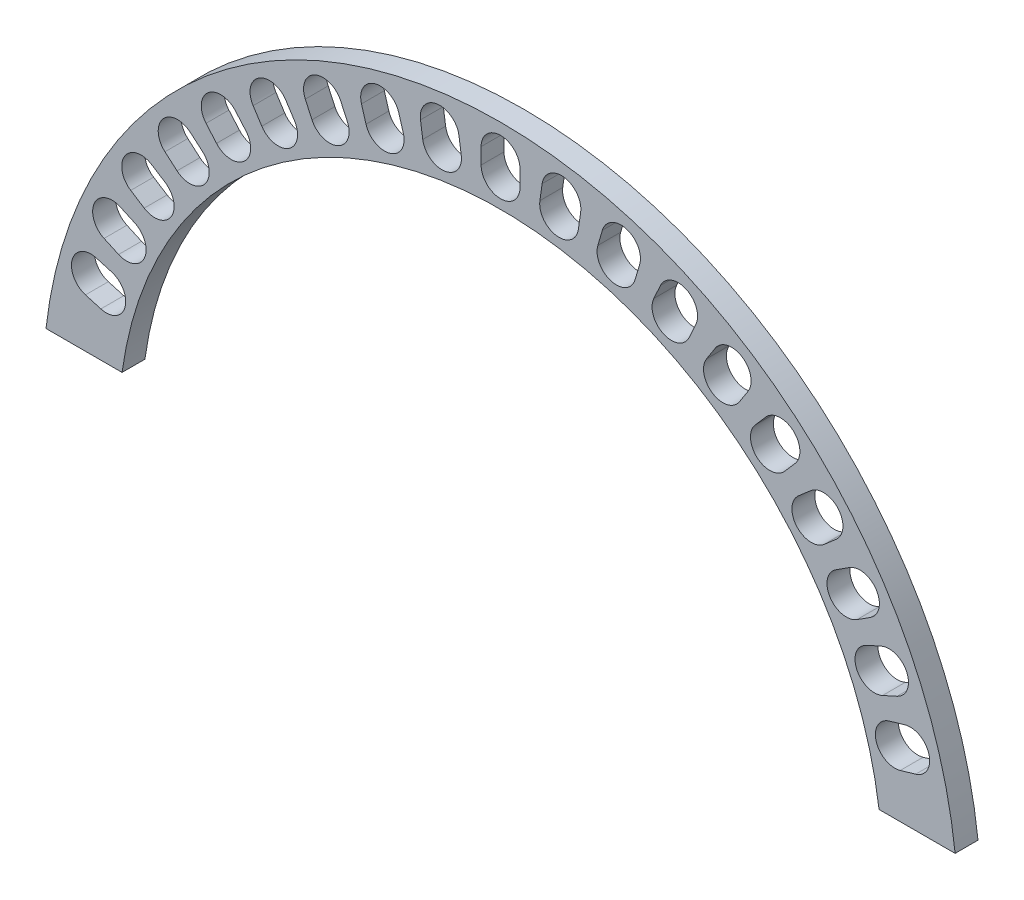
SolidWorks part; units mm, degrees
material "Acier allié"
ref_plane "Plan de face" through (0, 0, 0) normal (0, 0, 1) x (1, 0, 0)
ref_plane "Plan de dessus" through (0, 0, 0) normal (0, 1, 0) x (1, 0, 0)
ref_plane "Plan de droite" through (0, 0, 0) normal (1, 0, 0) x (0, 0, -1)
sketch "Esquisse1" plane through (0, 0, 0) normal (0, 0, 1) x (1, 0, 0)
  line L0 (0, 0) -> (117.1967, 0) construction
  line L1 (0, 22.5) -> (117.1967, 22.5) construction
  line L2 (-140.132, 22.5) -> (-106.879, 22.5)
  line L3 (224.0757, 22.5) -> (257.3287, 22.5)
  arc A0 (-106.879, 22.5) -> (224.0757, 22.5) centre (58.5983, 0) cw
  arc A1 (-140.132, 22.5) -> (257.3287, 22.5) centre (58.5983, 0) cw
  dimension "D2" = 200
  dimension "D3" = 167
  dimension "D1" = 22.5
extrude "Boss.-Extru.1" add sketch "Esquisse1" along normal blind 10
sketch "Esquisse2" plane through (0, 0, 10) normal (0, 0, 1) x (1, 0, 0)
  line L0 (58.5983, 0) -> (58.5983, 12) construction
  line L2 (50.0983, 179.5) -> (67.0983, 179.5) construction
  line L3 (50.0983, 179.5) -> (50.0983, 186.5)
  line L4 (50.0983, 186.5) -> (67.0983, 186.5) construction
  line L5 (67.0983, 179.5) -> (67.0983, 186.5)
  line L6 (50.0983, 179.5) -> (67.0983, 186.5) construction
  line L7 (50.0983, 186.5) -> (67.0983, 179.5) construction
  arc A0 (224.0757, 22.5) -> (-106.879, 22.5) centre (58.5983, 0) ccw
  arc A1 (224.0757, 22.5) -> (-106.879, 22.5) centre (58.5983, 0) ccw construction
  arc A2 (67.0983, 186.5) -> (50.0983, 186.5) centre (58.5983, 186.5) ccw
  arc A3 (50.0983, 179.5) -> (67.0983, 179.5) centre (58.5983, 179.5) ccw
  point P0 (58.5983, 183)
  dimension "D1" = 7
  dimension "D2" = 17
  dimension "D3" = 183
extrude "Enlèv. mat.-Extru.1" cut sketch "Esquisse2" against normal through all
pattern_circular "Répétition circulaire1" count 10 every 8.2 about axis through (58.5983, 0, 0) along (0, 0, 1) of "Enlèv. mat.-Extru.1"
pattern_circular "Répétition circulaire2" count 10 every 8.2 about axis through (58.5983, 0, 0) along (0, 0, 1) of "Enlèv. mat.-Extru.1"
